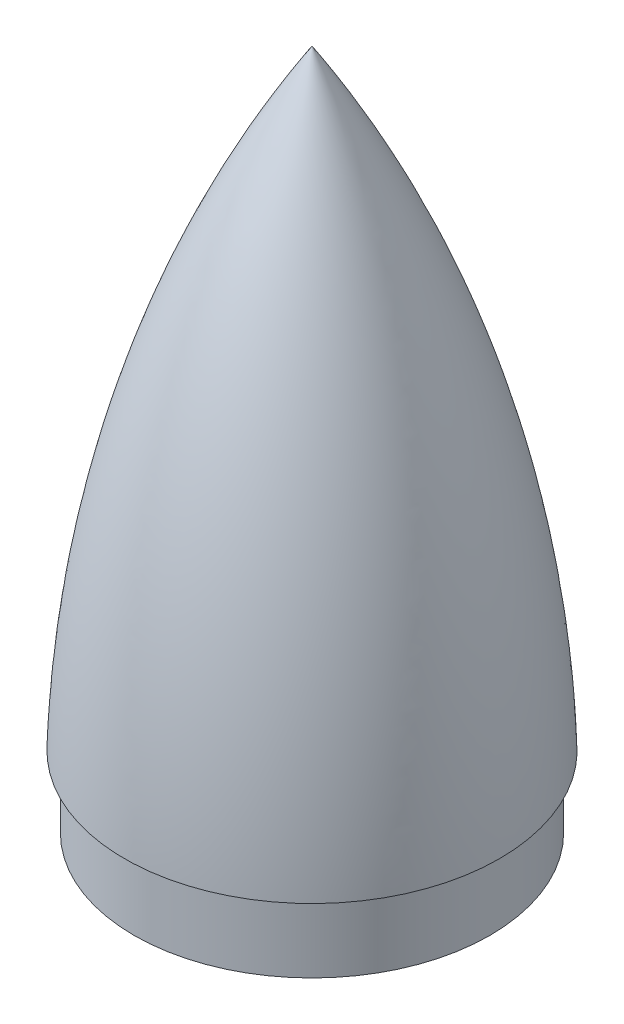
SolidWorks part; units mm, degrees
ref_plane "Front Plane" through (0, 0, 0) normal (0, 0, 1) x (1, 0, 0)
ref_plane "Top Plane" through (0, 0, 0) normal (0, 1, 0) x (1, 0, 0)
ref_plane "Right Plane" through (0, 0, 0) normal (1, 0, 0) x (0, 0, -1)
sketch "Sketch2" plane through (0, 0, 0) normal (0, 0, 1) x (1, 0, 0)
  line L0 (0, 0) -> (0, 304.8) construction
  line L1 (-93.6498, 0) -> (-88.9, 0)
  line L2 (0, 304.8) -> (0, 299.72)
  arc A0 (0, 304.8) -> (-93.6498, 0) centre (507.5687, -17.9374) ccw
  arc A1 (0, 299.72) -> (-88.9, 0) centre (553.2478, -27.4232) ccw
  dimension "D1" = 304.8
  dimension "D2" = 5.08
  dimension "D3" = 4.7498
  dimension "D4" = 88.9
revolve "Revolve1" add sketch "Sketch2" angle 360 about L2
sketch "Sketch3" plane through (0, 0, 0) normal (0, -1, 0) x (1, 0, 0)
  circle A0 centre (0, 0) radius 88.9
  circle A1 centre (0, 0) radius 86.995
  dimension "D1" = 177.8
extrude "Boss-Extrude1" add sketch "Sketch3" along normal blind 35.56
equation "\"D4@Sketch2\"=3.5"
